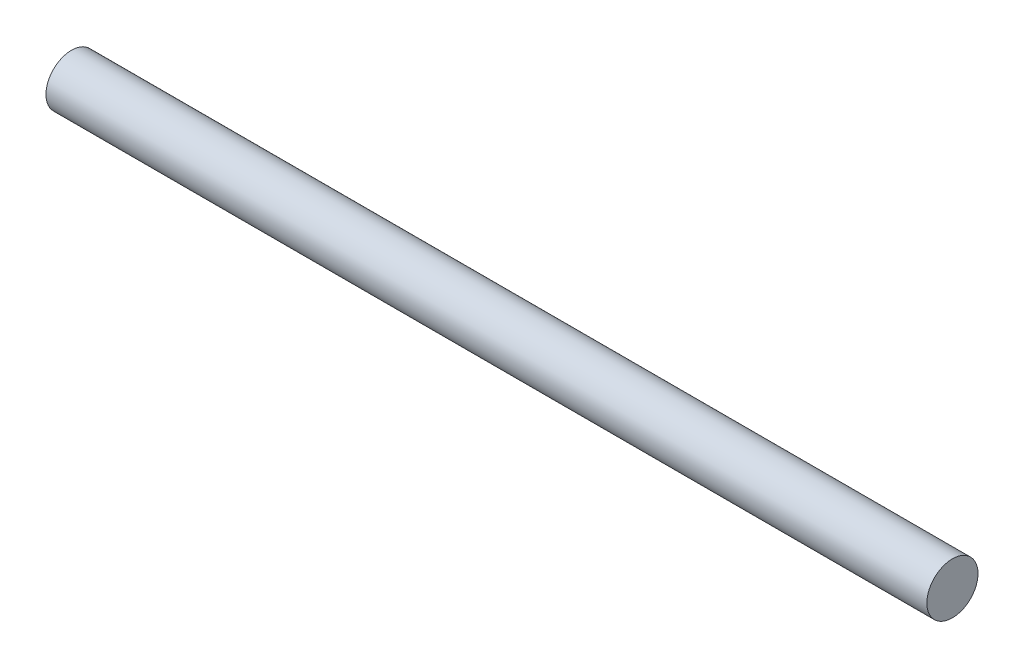
SolidWorks part; units mm, degrees
ref_plane "Plan de face" through (0, 0, 0) normal (0, 0, 1) x (1, 0, 0)
ref_plane "Plan de dessus" through (0, 0, 0) normal (0, 1, 0) x (1, 0, 0)
ref_plane "Plan de droite" through (0, 0, 0) normal (1, 0, 0) x (0, 0, -1)
sketch "Esquisse5" plane through (0, 0, 0) normal (1, 0, 0) x (0, 0, -1)
  circle A0 centre (0, 0) radius 18
extrude "Boss.-Extru.3" add sketch "Esquisse5" along normal blind 620
ref_plane "Plan2" through (10, 0, 0) normal (-1, 0, 0) x (0, 0, 1)
ref_plane "Plan4" through (610, 0, 0) normal (-1, 0, 0) x (0, 0, 1)
sketch "Esquisse6" plane through (10, 0, 0) normal (-1, 0, 0) x (0, 0, 1)
  circle A0 centre (0, 0) radius 18
sketch "Esquisse7" plane through (610, 0, 0) normal (-1, 0, 0) x (0, 0, 1)
  circle A0 centre (0, 0) radius 18
ref_plane "Plan31" through (490, 0, 0) normal (-1, 0, 0) x (0, 0, 1)
sketch "Esquisse32" plane through (490, 0, 0) normal (-1, 0, 0) x (0, 0, 1)
  circle A0 centre (0, 0) radius 18
ref_plane "Plan47" through (370, 0, 0) normal (-1, 0, 0) x (0, 0, 1)
ref_plane "Plan48" through (250, 0, 0) normal (-1, 0, 0) x (0, 0, 1)
ref_plane "Plan49" through (130, 0, 0) normal (-1, 0, 0) x (0, 0, 1)
sketch "Esquisse50" plane through (370, 0, 0) normal (-1, 0, 0) x (0, 0, 1)
  circle A0 centre (0, 0) radius 18
sketch "Esquisse51" plane through (250, 0, 0) normal (-1, 0, 0) x (0, 0, 1)
  circle A0 centre (0, 0) radius 18
sketch "Esquisse52" plane through (130, 0, 0) normal (-1, 0, 0) x (0, 0, 1)
  circle A0 centre (0, 0) radius 18
